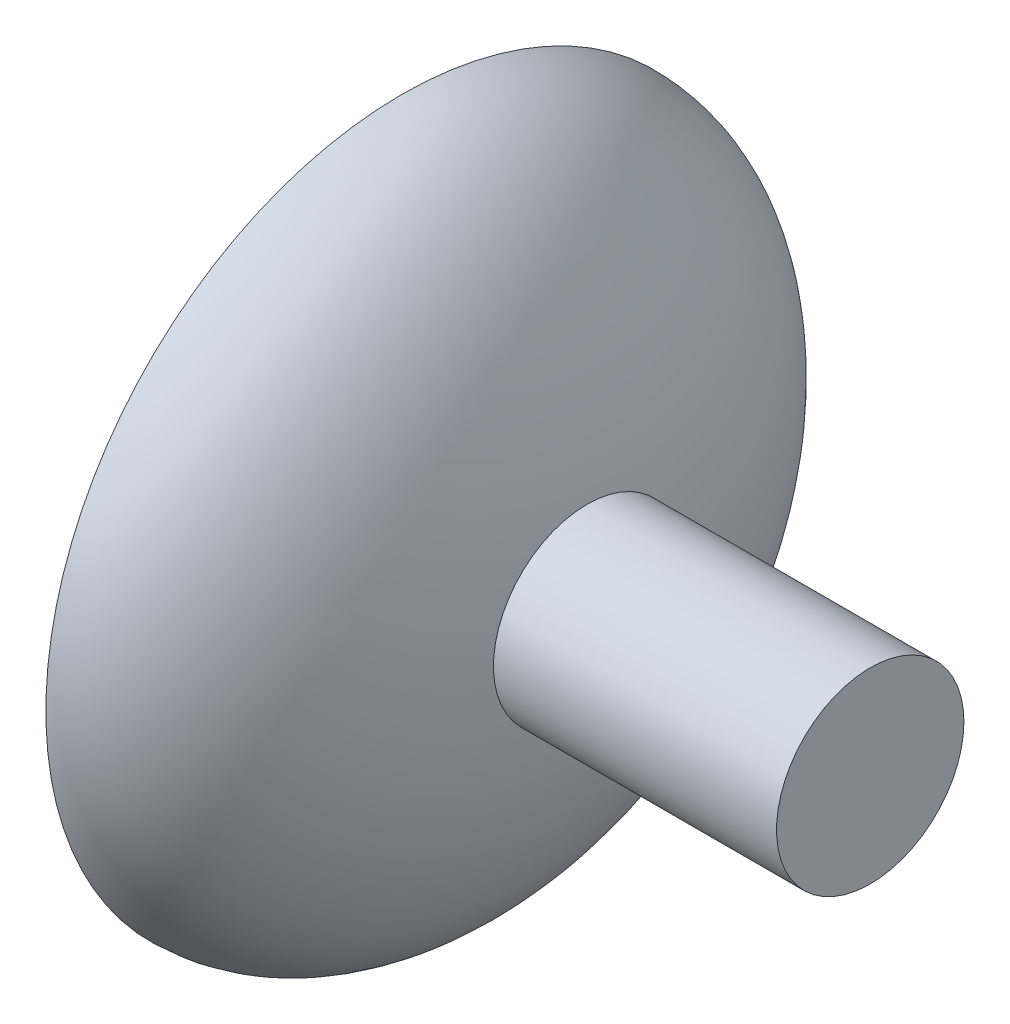
SolidWorks part; units mm, degrees
material "Acrylic (Medium-high impact)"
ref_plane "Front Plane" through (0, 0, 0) normal (0, 0, 1) x (1, 0, 0)
ref_plane "Top Plane" through (0, 0, 0) normal (0, 1, 0) x (1, 0, 0)
ref_plane "Right Plane" through (0, 0, 0) normal (1, 0, 0) x (0, 0, -1)
sketch "Sketch1" plane through (0, 0, 0) normal (0, 0, 1) x (1, 0, 0)
  line L0 (0, -48.26) -> (0, -38.1)
  line L1 (0, 38.1) -> (0, 48.26)
  line L2 (0, 0) -> (0, 48.26) construction
  line L3 (-26.035, 0) -> (-15.875, 0)
  ellipse E0 centre (0, 0) end of major axis (0, -38.1) minor radius 15.875 (0, 38.1) -> (0, -38.1) ccw
  ellipse E1 centre (0, 0) end of major axis (0, -48.26) minor radius 26.035 (0, 48.26) -> (0, -48.26) ccw
  point P4 (0, 0)
  dimension "D1" = 15.875
  dimension "D2" = 38.1
  dimension "D3" = 26.035
  dimension "D4" = 48.26
revolve "Revolve2" add sketch "Sketch1" angle 360 about L3
ref_plane "Plane1" through (0, -34.29, 0) normal (0, 1, 0) x (1, 0, 0)
ref_plane "Plane2" through (0, -45.212, 0) normal (0, 1, 0) x (1, 0, 0)
sketch "Sketch2" plane through (0, -34.29, 0) normal (0, 1, 0) x (1, 0, 0)
  line L0 (0, -48.26) -> (0, 48.26) construction
  line L1 (0, 7.699) -> (-6.6675, -3.8495)
  line L2 (-6.6675, -3.8495) -> (6.6675, -3.8495)
  line L3 (6.6675, -3.8495) -> (0, 7.699)
  circle A0 centre (0, 0) radius 3.8495 construction
  dimension "D1" = 13.335
sketch "Sketch3" plane through (0, -45.212, 0) normal (0, 1, 0) x (1, 0, 0)
  point P0 (0, 0)
loft "Cut-Loft1" cut profiles "Sketch2", "Sketch3"
pattern_circular "CirPattern1" count 12 over 360 about axis through (0, 0, 0) along (1, 0, 0) of "Cut-Loft1"
sketch "Sketch6" plane through (0, 0, 0) normal (1, 0, 0) x (0, 0, -1)
  line L0 (8.5266, 37.1336) -> (-8.5266, -37.1336) construction
  line L1 (8.5266, 37.1336) -> (10.8004, 47.0359) construction
  line L2 (-8.5266, -37.1336) -> (-10.8004, -47.0359) construction
  line L3 (5.0218, 43.1506) -> (14.3052, 41.019)
  line L4 (4.8512, 42.4079) -> (14.1347, 40.2763)
  line L5 (5.1923, 43.8933) -> (14.4757, 41.7616)
  line L6 (5.1923, 43.8933) -> (4.8512, 42.4079)
  line L7 (14.4757, 41.7616) -> (14.1347, 40.2763)
  line L8 (0, 0) -> (16.9193, -3.885) construction
  arc A0 (14.3014, 35.314) -> (2.5364, 38.0155) centre (0, 0) ccw construction
  arc A1 (-14.3014, -35.314) -> (-2.5364, -38.0155) centre (0, 0) ccw construction
  circle A2 centre (0, 0) radius 48.26 construction
  point P15 (9.6635, 42.0848)
  dimension "D1" = 9.525
  dimension "D2" = 0.762
  dimension "D3" = 0.762
mirror "Mirror5" about plane through (0, 0, 0) normal (1, 0, 0) of bodies 106 109
delete or keep bodies "Body-Delete/Keep 2" bodies 106
extrude "Cut-Extrude1" cut sketch "Sketch6" along normal blind 4.572 contours L5 L7 L4 L6
sketch "Sketch7" plane through (0, -1.0658, -4.6417) normal (0, 0.2238, 0.9746) x (1, 0, 0)
  line L2 (4.572, 42.418) -> (4.572, 40.894)
  line L3 (4.572, 40.894) -> (3.048, 40.894)
  line L4 (3.048, 40.894) -> (3.048, 42.418)
  line L5 (3.048, 42.418) -> (4.572, 42.418)
  dimension "D1" = 1.524
  dimension "D2" = 1.524
extrude "Cut-Extrude2" cut sketch "Sketch7" along normal up to surface (9.525 mm away) up to face at (2.286, 43.1506, -5.0218)
ref_plane "Plane3" through (0, 0, 0) normal (0, -0.9746, 0.2238) x (-1, 0, 0)
mirror "Mirror6" about plane through (0, 0, 0) normal (0, -0.9746, 0.2238) of "Cut-Extrude2", "Cut-Extrude1"
ref_plane "Plane4" through (63.5, 0, 0) normal (1, 0, 0) x (0, 0, -1)
sketch "Sketch8" plane through (63.5, 0, 0) normal (1, 0, 0) x (0, 0, -1)
  circle A0 centre (0, 0) radius 12.7
  dimension "D1" = 25.4
extrude "Boss-Extrude1" add sketch "Sketch8" against normal up to surface (38.3827 mm away)
